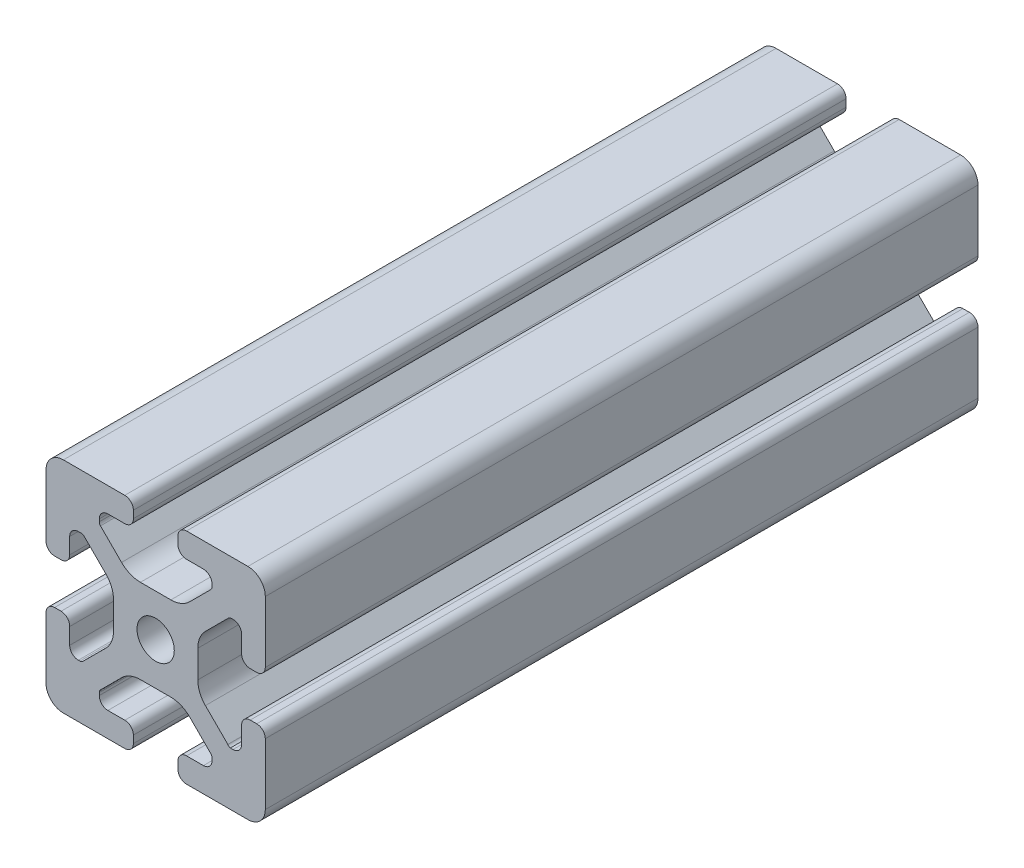
SolidWorks part; units mm, degrees
material "6105-T5 Aluminum"
ref_plane "Front Plane" through (0, 0, 0) normal (0, 0, 1) x (1, 0, 0)
ref_plane "Top Plane" through (0, 0, 0) normal (0, 1, 0) x (1, 0, 0)
ref_plane "Right Plane" through (0, 0, 0) normal (1, 0, 0) x (0, 0, -1)
sketch "Sketch1" plane through (0, 0, 0) normal (0, 0, 1) x (1, 0, 0)
  line L0 (0, 19.7407) -> (0, -19.7407) construction
  line L1 (19.0335, 0) -> (-20.7246, 0) construction
  line L2 (-8.715, -15.5246) -> (-5.63, -15.5246)
  line L3 (-10.285, -13.9546) -> (-10.285, -13.4925)
  line L4 (-6.2171, -9.1098) -> (-10.0624, -12.9551)
  line L5 (2.7773, -7.685) -> (-2.7773, -7.685)
  line L6 (10.0624, -12.9551) -> (6.2171, -9.1098)
  line L7 (10.285, -13.9546) -> (10.285, -13.4925)
  line L8 (5.63, -15.5246) -> (8.715, -15.5246)
  line L9 (4.06, -18.43) -> (4.06, -17.0946)
  line L10 (-4.06, -18.43) -> (-4.06, -17.0946)
  line L11 (15.68, -8.7154) -> (15.68, -5.63)
  line L12 (-14.11, -10.2854) -> (-13.8169, -10.2854)
  line L13 (20, -16.83) -> (20, -5.63)
  line L14 (20, 5.63) -> (20, 13.0011)
  line L15 (-16.83, 20) -> (-5.63, 20)
  line L16 (5.63, 20) -> (12.9796, 20)
  line L18 (-8.715, 15.5246) -> (-5.63, 15.5246)
  line L19 (-20, -17.0184) -> (-20, -5.7579)
  line L20 (-20, 5.573) -> (-20, 13.0045)
  line L21 (-15.68, -8.7154) -> (-15.68, -5.7579)
  line L23 (-16.6746, -20) -> (-5.63, -20)
  line L24 (5.63, -20) -> (13, -20)
  line L53 (14.11, -10.2854) -> (13.6201, -10.2854)
  line L54 (13.1637, -9.947) -> (9.0762, -5.8595)
  line L55 (7.685, -2.5008) -> (7.685, 2.5008)
  line L56 (9.0762, 5.8595) -> (13.2795, 10.0628)
  line L57 (13.8169, 10.2854) -> (14.11, 10.2854)
  line L58 (15.68, 8.7154) -> (15.68, 5.63)
  line L59 (17.25, 4.06) -> (18.43, 4.06)
  line L61 (20, 13.0011) -> (20, 16.83)
  line L62 (16.83, 20) -> (12.9796, 20)
  line L64 (4.06, 18.43) -> (4.06, 17.0946)
  line L65 (5.63, 15.5246) -> (8.715, 15.5246)
  line L66 (10.285, 13.9546) -> (10.285, 13.4925)
  line L67 (10.0624, 12.9551) -> (6.2171, 9.1098)
  line L68 (2.7773, 7.685) -> (-2.7773, 7.685)
  line L69 (-6.2171, 9.1098) -> (-10.0624, 12.9551)
  line L70 (-10.285, 13.4925) -> (-10.285, 13.9546)
  line L72 (-4.06, 17.0946) -> (-4.06, 18.43)
  line L75 (-20, 16.83) -> (-20, 13.0045)
  line L77 (-18.43, 4.003) -> (-17.25, 4.003)
  line L78 (-15.68, 5.573) -> (-15.68, 8.4757)
  line L79 (-14.0552, 10.0447) -> (-13.7199, 10.033)
  line L80 (-13.0405, 9.8238) -> (-9.0762, 5.8595)
  line L81 (-7.685, 2.5008) -> (-7.685, -2.5008)
  line L82 (-9.0762, -5.8595) -> (-13.2795, -10.0628)
  line L85 (-17.25, -4.1204) -> (-18.43, -4.1204)
  line L100 (13, -20) -> (16.83, -20)
  line L103 (18.43, -4.06) -> (17.25, -4.06)
  arc A0 (-5.63, -15.5246) -> (-4.06, -17.0946) centre (-5.63, -17.0946) cw
  arc A1 (-8.715, -15.5246) -> (-10.285, -13.9546) centre (-8.715, -13.9546) cw
  arc A2 (-10.285, -13.4925) -> (-10.0624, -12.9551) centre (-9.525, -13.4925) cw
  arc A3 (-6.2171, -9.1098) -> (-2.7773, -7.685) centre (-2.7773, -12.5496) cw
  arc A4 (2.7773, -7.685) -> (6.2171, -9.1098) centre (2.7773, -12.5496) cw
  arc A5 (10.0624, -12.9551) -> (10.285, -13.4925) centre (9.525, -13.4925) cw
  arc A6 (10.285, -13.9546) -> (8.715, -15.5246) centre (8.715, -13.9546) cw
  arc A7 (4.06, -17.0946) -> (5.63, -15.5246) centre (5.63, -17.0946) cw
  arc A8 (5.63, -20) -> (4.06, -18.43) centre (5.63, -18.43) cw
  arc A9 (-4.06, -18.43) -> (-5.63, -20) centre (-5.63, -18.43) cw
  circle A45 centre (0, 0) radius 3.4
  arc A46 (17.25, -4.06) -> (15.68, -5.63) centre (17.25, -5.63) ccw
  arc A47 (14.11, -10.2854) -> (15.68, -8.7154) centre (14.11, -8.7154) ccw
  arc A48 (13.1637, -9.947) -> (13.6201, -10.2854) centre (13.8117, -9.55) ccw
  arc A49 (7.685, -2.5008) -> (9.0762, -5.8595) centre (12.435, -2.5008) ccw
  arc A50 (9.0762, 5.8595) -> (7.685, 2.5008) centre (12.435, 2.5008) ccw
  arc A51 (13.8169, 10.2854) -> (13.2795, 10.0628) centre (13.8169, 9.5254) ccw
  arc A52 (15.68, 8.7154) -> (14.11, 10.2854) centre (14.11, 8.7154) ccw
  arc A53 (15.68, 5.63) -> (17.25, 4.06) centre (17.25, 5.63) ccw
  arc A54 (18.43, 4.06) -> (20, 5.63) centre (18.43, 5.63) ccw
  arc A55 (20, 16.83) -> (16.83, 20) centre (16.83, 16.83) ccw
  arc A56 (5.63, 20) -> (4.06, 18.43) centre (5.63, 18.43) ccw
  arc A57 (4.06, 17.0946) -> (5.63, 15.5246) centre (5.63, 17.0946) ccw
  arc A58 (10.285, 13.9546) -> (8.715, 15.5246) centre (8.715, 13.9546) ccw
  arc A59 (10.0624, 12.9551) -> (10.285, 13.4925) centre (9.525, 13.4925) ccw
  arc A60 (2.7773, 7.685) -> (6.2171, 9.1098) centre (2.7773, 12.5496) ccw
  arc A61 (-6.2171, 9.1098) -> (-2.7773, 7.685) centre (-2.7773, 12.5496) ccw
  arc A62 (-10.285, 13.4925) -> (-10.0624, 12.9551) centre (-9.525, 13.4925) ccw
  arc A63 (-8.715, 15.5246) -> (-10.285, 13.9546) centre (-8.715, 13.9546) ccw
  arc A64 (-5.63, 15.5246) -> (-4.06, 17.0946) centre (-5.63, 17.0946) ccw
  arc A65 (-4.06, 18.43) -> (-5.63, 20) centre (-5.63, 18.43) ccw
  arc A66 (-16.83, 20) -> (-20, 16.83) centre (-16.83, 16.83) ccw
  arc A67 (-20, 5.573) -> (-18.43, 4.003) centre (-18.43, 5.573) ccw
  arc A68 (-17.25, 4.003) -> (-15.68, 5.573) centre (-17.25, 5.573) ccw
  arc A69 (-14.0552, 10.0447) -> (-15.68, 8.4757) centre (-14.11, 8.4757) ccw
  arc A70 (-13.0405, 9.8238) -> (-13.7199, 10.033) centre (-13.5779, 9.2864) ccw
  arc A71 (-7.685, 2.5008) -> (-9.0762, 5.8595) centre (-12.435, 2.5008) ccw
  arc A72 (-9.0762, -5.8595) -> (-7.685, -2.5008) centre (-12.435, -2.5008) ccw
  arc A73 (-13.8169, -10.2854) -> (-13.2795, -10.0628) centre (-13.8169, -9.5254) ccw
  arc A74 (-15.68, -8.7154) -> (-14.11, -10.2854) centre (-14.11, -8.7154) ccw
  arc A75 (-15.68, -5.7579) -> (-17.25, -4.1204) centre (-17.2485, -5.6904) ccw
  arc A76 (-18.43, -4.1204) -> (-20, -5.7579) centre (-18.4315, -5.6904) ccw
  arc A77 (-20, -17.0184) -> (-16.6746, -20) centre (-16.8354, -16.8341) ccw
  arc A88 (16.83, -20) -> (20, -16.83) centre (16.83, -16.83) ccw
  arc A89 (20, -5.63) -> (18.43, -4.06) centre (18.43, -5.63) ccw
  dimension "D2" = 6.8
  dimension "D7" = 20.57
  dimension "D1" = 40
  dimension "D3" = 4.32
  dimension "D4" = 15.37
  dimension "D5" = 20
  dimension "D6" = 4.32
  dimension "D9" = 15.37
extrude "Extrude1" add sketch "Sketch1" against normal blind 130
